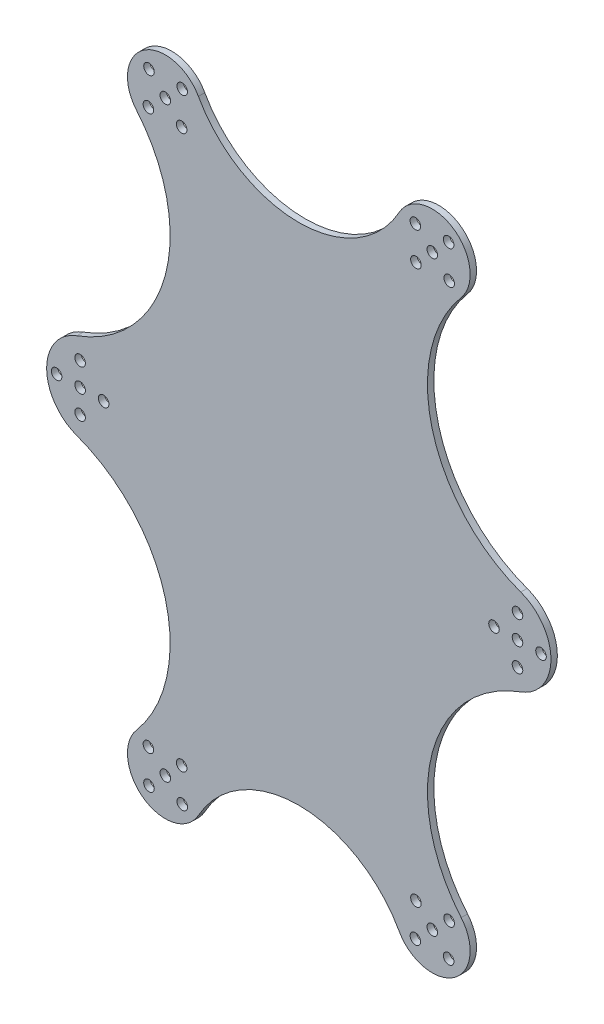
SolidWorks part; units mm, degrees
ref_plane "前视基准面" through (0, 0, 0) normal (0, 0, 1) x (1, 0, 0)
ref_plane "上视基准面" through (0, 0, 0) normal (0, 1, 0) x (1, 0, 0)
ref_plane "右视基准面" through (0, 0, 0) normal (1, 0, 0) x (0, 0, -1)
sketch "草图1" plane through (0, 0, 0) normal (0, 0, 1) x (1, 0, 0)
  line L0 (4.4926, -1.2596) -> (4.4926, -27.7633) construction
  line L1 (109.289, 84.436) -> (119.8633, 74.2245) construction
  line L2 (-7.014, -12.3723) -> (212.2703, -12.3723) construction
  line L3 (26.0221, 84.6174) -> (36.2336, 74.0431) construction
  line L4 (36.415, 84.436) -> (25.8407, 74.2245) construction
  line L5 (72.852, 157.0661) -> (72.852, -150.5607) construction
  line L6 (119.6818, 84.6174) -> (109.4704, 74.0431) construction
  line L7 (141.2114, -1.2596) -> (141.2114, -27.7633) construction
  line L8 (119.6818, -109.362) -> (109.4704, -98.7877) construction
  line L9 (36.415, -109.1806) -> (25.8407, -98.9691) construction
  line L10 (26.0221, -109.362) -> (36.2336, -98.7877) construction
  line L11 (109.289, -109.1806) -> (119.8633, -98.9691) construction
  circle A0 centre (11.8426, -12.3723) radius 1.65
  arc A1 (3.4788, 1.1401) -> (22.098, 71.5511) centre (-11.7565, 42.8361) ccw
  arc A2 (22.0964, 71.553) -> (41.4673, 84.9489) centre (31.1278, 79.1967) cw
  arc A3 (41.4673, 84.9489) -> (104.2366, 84.9489) centre (72.852, 102.4092) ccw
  arc A4 (22.098, 71.5511) -> (22.0964, 71.553) centre (23.8782, 73.061) cw
  circle A5 centre (119.6818, 84.6174) radius 1.65
  circle A6 centre (36.415, 84.436) radius 1.65
  circle A7 centre (36.2336, 74.0431) radius 1.65
  circle A8 centre (4.4926, -19.7223) radius 1.65
  circle A9 centre (114.5761, 79.3303) radius 1.65
  circle A10 centre (119.8633, 74.2245) radius 1.65
  circle A11 centre (141.2114, -5.0223) radius 1.65
  circle A12 centre (109.4704, 74.0431) radius 1.65
  circle A13 centre (148.5614, -12.3723) radius 1.65
  circle A14 centre (141.2114, -19.7223) radius 1.65
  circle A15 centre (141.2114, -12.3723) radius 1.65
  circle A16 centre (109.289, 84.436) radius 1.65
  circle A17 centre (133.8614, -12.3723) radius 1.65
  circle A18 centre (141.2114, -5.0223) radius 1.65
  arc A19 (142.2251, -25.8847) -> (142.2251, 1.1401) centre (137.2878, -12.3723) ccw
  arc A20 (123.6059, 71.5511) -> (123.6075, 71.553) centre (121.8257, 73.061) ccw
  arc A21 (123.6075, 71.553) -> (104.2366, 84.9489) centre (114.5761, 79.1967) ccw
  arc A22 (142.2251, 1.1401) -> (123.6059, 71.5511) centre (157.4605, 42.8361) cw
  circle A23 centre (4.4926, -5.0223) radius 1.65
  circle A24 centre (26.0221, -109.362) radius 1.65
  circle A25 centre (31.1278, -104.0749) radius 1.65
  circle A26 centre (25.8407, -98.9691) radius 1.65
  circle A27 centre (25.8407, 74.2245) radius 1.65
  circle A28 centre (31.1278, 79.3303) radius 1.65
  circle A29 centre (26.0221, 84.6174) radius 1.65
  arc A30 (142.2251, -25.8847) -> (123.6059, -96.2957) centre (157.4605, -67.5808) ccw
  arc A31 (123.6075, -96.2976) -> (104.2366, -109.6935) centre (114.5761, -103.9413) cw
  arc A32 (123.6059, -96.2957) -> (123.6075, -96.2976) centre (121.8257, -97.8056) cw
  circle A33 centre (109.289, -109.1806) radius 1.65
  circle A34 centre (109.4704, -98.7877) radius 1.65
  circle A35 centre (119.8633, -98.9691) radius 1.65
  circle A36 centre (114.5761, -104.0749) radius 1.65
  circle A37 centre (36.2336, -98.7877) radius 1.65
  circle A38 centre (36.415, -109.1806) radius 1.65
  circle A39 centre (119.6818, -109.362) radius 1.65
  arc A40 (22.098, -96.2957) -> (22.0964, -96.2976) centre (23.8782, -97.8056) ccw
  arc A41 (41.4673, -109.6935) -> (104.2366, -109.6935) centre (72.852, -127.1538) cw
  arc A42 (22.0964, -96.2976) -> (41.4673, -109.6935) centre (31.1278, -103.9413) ccw
  arc A43 (3.4788, -25.8847) -> (22.098, -96.2957) centre (-11.7565, -67.5808) cw
  circle A80 centre (-2.8574, -12.3723) radius 1.65
  circle A81 centre (4.4926, -12.3723) radius 1.65
  arc A104 (3.4788, -25.8847) -> (3.4788, 1.1401) centre (8.4161, -12.3723) cw
  dimension "D1" = 14.7
  dimension "D2" = 14.7
  dimension "D3" = 14.7
  dimension "D4" = 14.7
extrude "凸台-拉伸1" add sketch "草图1" along normal blind 2
